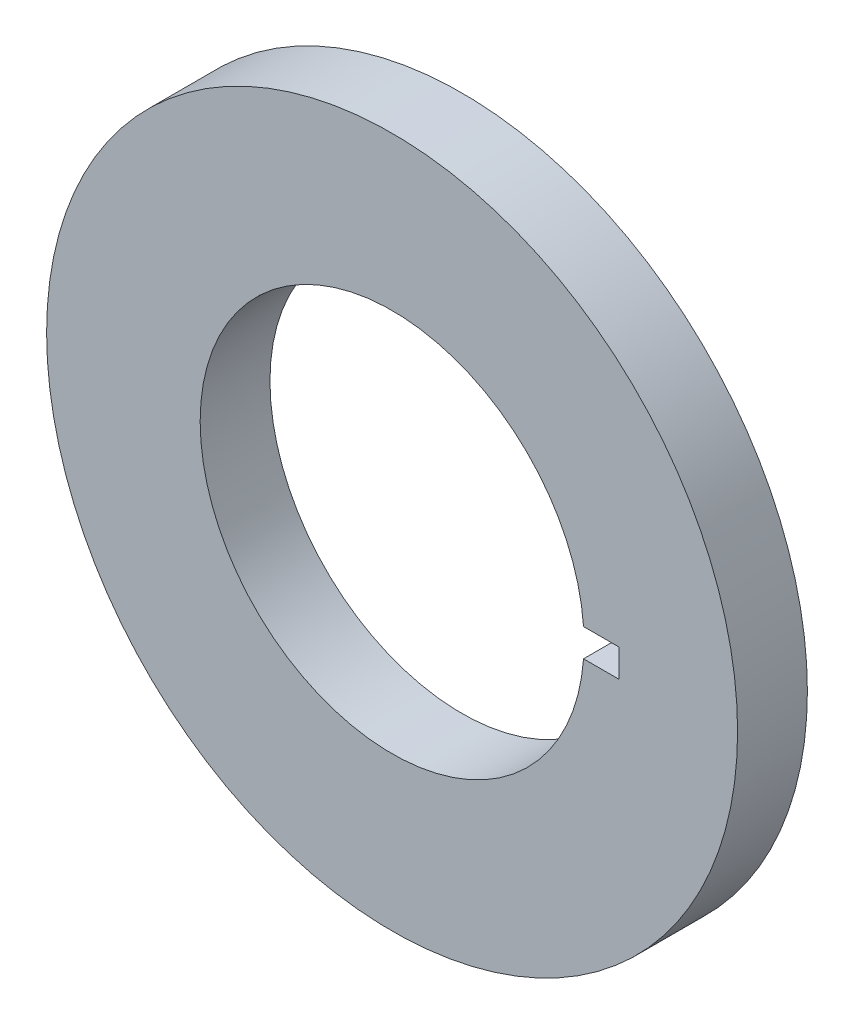
SolidWorks part; units mm, degrees
ref_plane "正面" through (0, 0, 0) normal (0, 0, 1) x (1, 0, 0)
ref_plane "平面" through (0, 0, 0) normal (0, 1, 0) x (1, 0, 0)
ref_plane "右側面" through (0, 0, 0) normal (1, 0, 0) x (0, 0, -1)
sketch "Sketch1" plane through (0, 0, 0) normal (0, 0, 1) x (1, 0, 0)
  circle A0 centre (0, 0) radius 49.5
  circle A1 centre (0, 0) radius 27.5
  dimension "D1" = 55
  dimension "D2" = 99
extrude "Boss-Extrude1" add sketch "Sketch1" along normal blind 10
sketch "Sketch2" plane through (0, 0, 10) normal (0, 0, 1) x (1, 0, 0)
  line L1 (22.5, 2) -> (32.5, 2)
  line L2 (22.5, 2) -> (22.5, -2)
  line L3 (22.5, -2) -> (32.5, -2)
  line L4 (32.5, 2) -> (32.5, -2)
  line L5 (22.5, 2) -> (32.5, -2) construction
  line L6 (22.5, -2) -> (32.5, 2) construction
  circle A0 centre (0, 0) radius 27.5 construction
  point P0 (27.5, 0)
  dimension "D1" = 4
  dimension "D2" = 10
extrude "Cut-Extrude1" cut sketch "Sketch2" against normal through all
